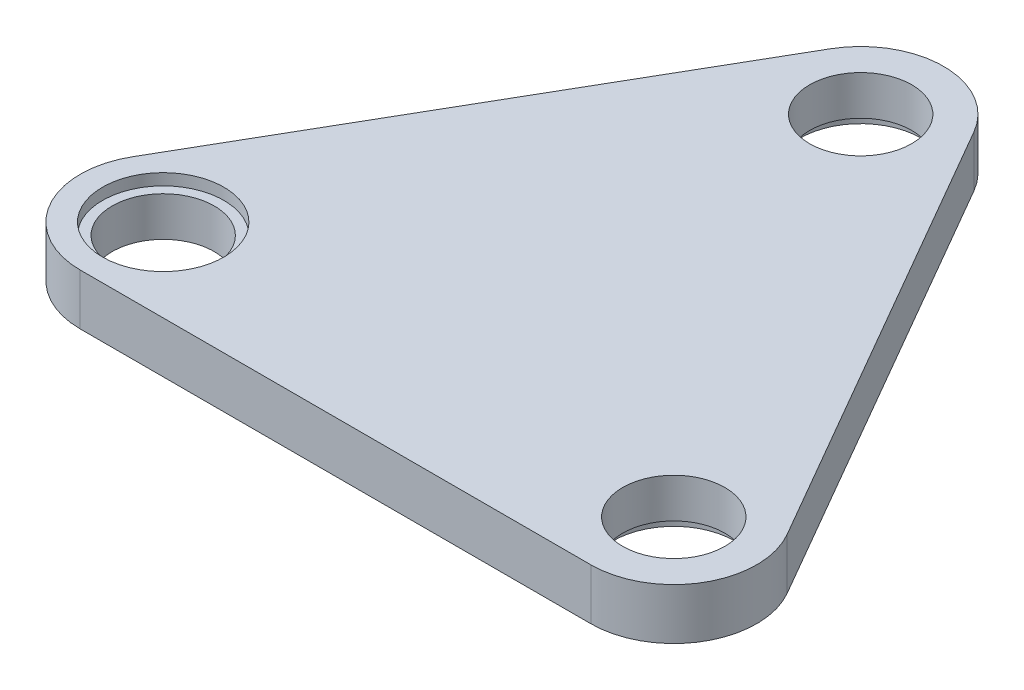
SolidWorks part; units mm, degrees
ref_plane "前视基准面" through (0, 0, 0) normal (0, 0, 1) x (1, 0, 0)
ref_plane "上视基准面" through (0, 0, 0) normal (0, 1, 0) x (1, 0, 0)
ref_plane "右视基准面" through (0, 0, 0) normal (1, 0, 0) x (0, 0, -1)
other "Configuration Table"
sketch "草图2" plane through (0, 0, 0) normal (0, 1, 0) x (1, 0, 0)
  line L0 (0, 0) -> (40, 0) construction
  line L1 (0, 6.5) -> (40, 6.5)
  line L2 (0, -6.5) -> (40, -6.5)
  line L3 (0, 0) -> (20, 34.641) construction
  line L4 (-5.6292, 3.25) -> (14.3708, 37.891)
  line L5 (5.6292, -3.25) -> (25.6292, 31.391)
  line L6 (20, 34.641) -> (40, 0) construction
  line L7 (25.6292, 37.891) -> (45.6292, 3.25)
  line L8 (14.3708, 31.391) -> (34.3708, -3.25)
  arc A0 (0, 6.5) -> (0, -6.5) centre (0, 0) ccw
  arc A1 (40, -6.5) -> (40, 6.5) centre (40, 0) ccw
  arc A2 (-5.6292, 3.25) -> (5.6292, -3.25) centre (0, 0) ccw
  arc A3 (25.6292, 31.391) -> (14.3708, 37.891) centre (20, 34.641) ccw
  arc A4 (25.6292, 37.891) -> (14.3708, 31.391) centre (20, 34.641) ccw
  arc A5 (34.3708, -3.25) -> (45.6292, 3.25) centre (40, 0) ccw
  point P3 (20, 0)
  point P8 (10, 17.3205)
  point P15 (30, 17.3205)
  point P22 (-46.485, 19.9068)
  dimension "D3" = 6.5
  dimension "D1" = 40
  dimension "D2" = 40
  dimension "D4" = 60
extrude "凸台-拉伸1" add sketch "草图2" along normal blind 4 contours A3 L5 L8 L1 A1 L7 | A5 L8 L1 L5 A2 L2 | L8 A5 A1 L1 | A4 L4 A0 L1 L5 L8 | A3 A4 L8 L5 | A0 A2 L5 L1 | L8 L5 L1
sketch "草图3" plane through (0, 4, 0) normal (0, 1, 0) x (1, 0, 0)
  point P0 (0, 0)
  point P3 (40, 0)
  point P6 (20, 34.641)
hole_wizard "M5 六角头螺栓的柱形沉头孔1" positions "草图3" profile "草图4" counterbore size "M5" standard "GB"
sketch "草图4" plane through (0, 4, 0) normal (1, 0, 0) x (0, 0, 1)
  line L0 (0, 0) -> (0, 14.8034)
  line L1 (0, 14.8034) -> (4, 12.4)
  line L2 (4, 12.4) -> (4, 0.9)
  line L3 (4, 0.9) -> (4.75, 0.9)
  line L4 (4.75, 0.9) -> (4.75, 0)
  line L5 (4.75, 0) -> (0, 0)
  line L10 (0, 14.8034) -> (-4, 12.4) construction
  line L11 (0, -6.35) -> (0, 107.95) construction
  dimension "孔直径" = 8
  dimension "孔深度" = 12.4
  dimension "柱形沉头孔直径" = 9.5
  dimension "柱形沉头孔深度" = 0.9
  dimension "导头角度" = 118
sketch "草图5" plane through (0, 0, 0) normal (0, -1, 0) x (-1, 0, 0)
  point P0 (-40, 0)
  point P3 (-20, 34.641)
hole_wizard "M5 六角头螺栓的柱形沉头孔2" positions "草图5" profile "草图6" counterbore size "M5" standard "GB"
sketch "草图6" plane through (40, 0, 0) normal (1, 0, 0) x (0, 0, -1)
  line L0 (0, 0) -> (0, 14.8034)
  line L1 (0, 14.8034) -> (4, 12.4)
  line L2 (4, 12.4) -> (4, 0.9)
  line L3 (4, 0.9) -> (4.75, 0.9)
  line L4 (4.75, 0.9) -> (4.75, 0)
  line L5 (4.75, 0) -> (0, 0)
  line L10 (0, 14.8034) -> (-4, 12.4) construction
  line L11 (0, -6.35) -> (0, 107.95) construction
  dimension "孔直径" = 8
  dimension "孔深度" = 12.4
  dimension "柱形沉头孔直径" = 9.5
  dimension "柱形沉头孔深度" = 0.9
  dimension "导头角度" = 118
